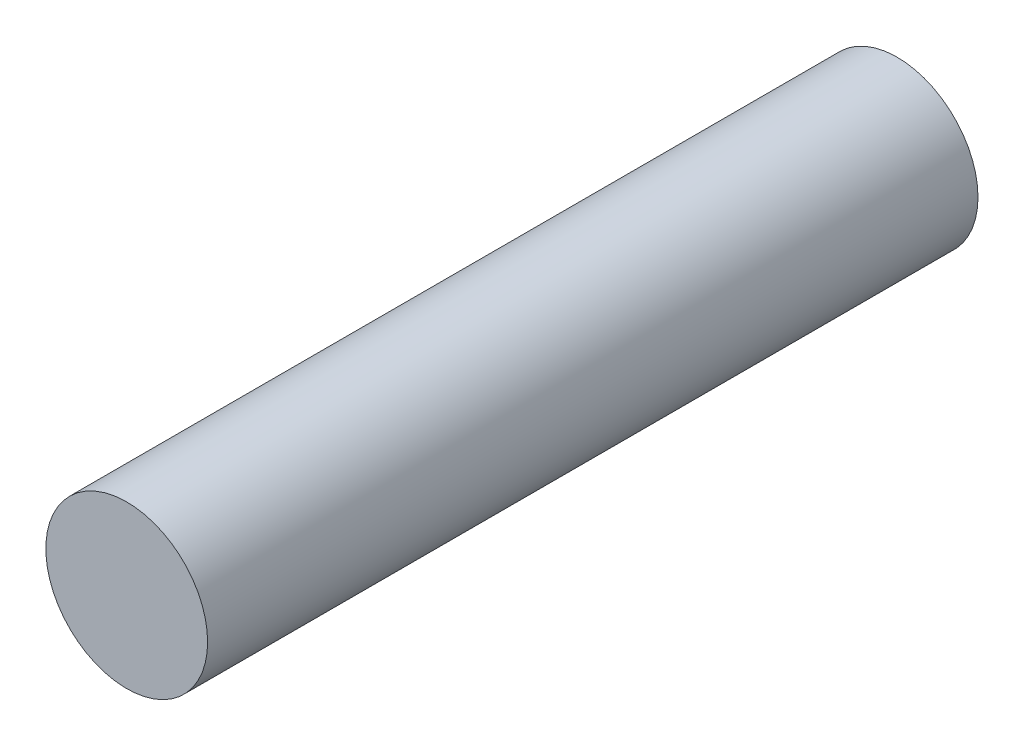
SolidWorks part; units mm, degrees
ref_plane "Front Plane" through (0, 0, 0) normal (0, 0, 1) x (1, 0, 0)
ref_plane "Top Plane" through (0, 0, 0) normal (0, 1, 0) x (1, 0, 0)
ref_plane "Right Plane" through (0, 0, 0) normal (1, 0, 0) x (0, 0, -1)
sketch "Sketch1" plane through (0, 0, 0) normal (0, 0, 1) x (1, 0, 0)
  circle A0 centre (0, 0) radius 1.05
  dimension "D1" = 2.1
extrude "Boss-Extrude1" add sketch "Sketch1" along normal blind 10
